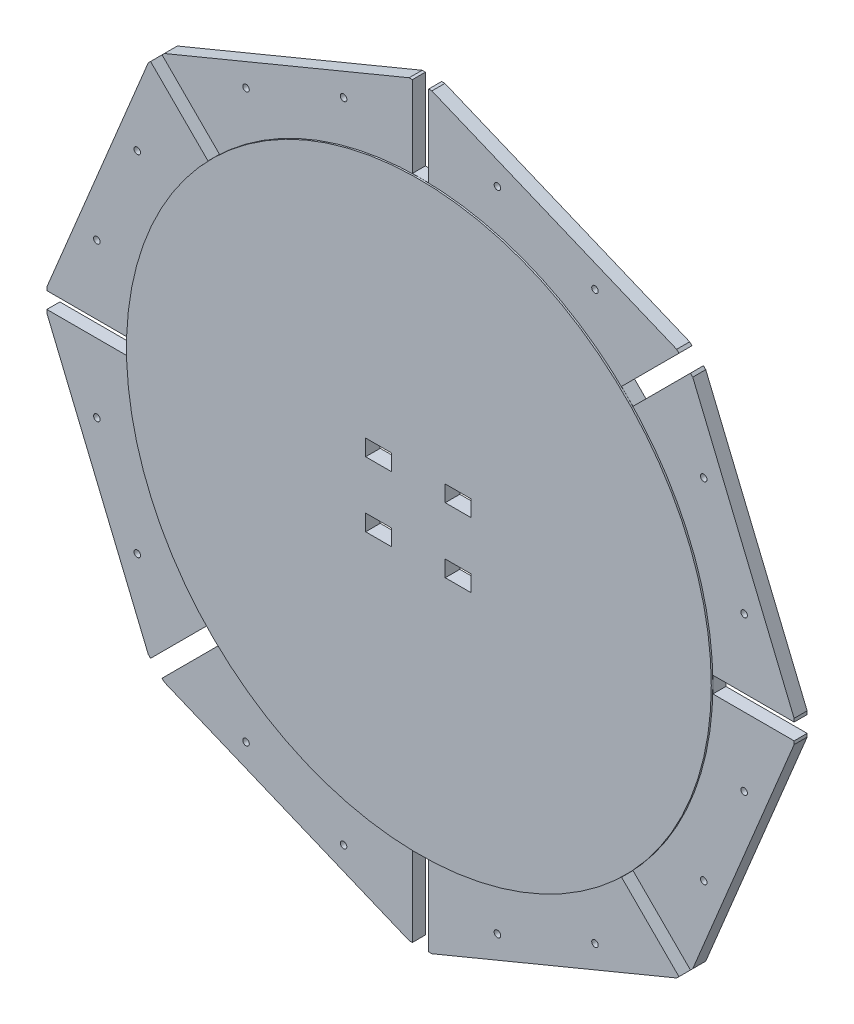
SolidWorks part; units mm, degrees
ref_plane "Front Plane" through (0, 0, 0) normal (0, 0, 1) x (1, 0, 0)
ref_plane "Top Plane" through (0, 0, 0) normal (0, 1, 0) x (1, 0, 0)
ref_plane "Right Plane" through (0, 0, 0) normal (1, 0, 0) x (0, 0, -1)
sketch "Sketch1" plane through (0, 0, 0) normal (0, 0, 1) x (1, 0, 0)
  line L0 (5, 230) -> (5, 180)
  line L1 (5, 180) -> (-5, 180)
  line L2 (-5, 180) -> (-5, 230)
  line L3 (-5, 230) -> (-7, 230)
  line L4 (-7, 230) -> (-157.6848, 167.5843)
  line L5 (-157.6848, 167.5843) -> (-159.099, 166.1701)
  line L6 (-159.099, 166.1701) -> (-123.7437, 130.8148)
  line L7 (-123.7437, 130.8148) -> (-130.8148, 123.7437)
  line L8 (-130.8148, 123.7437) -> (-166.1701, 159.099)
  line L9 (-166.1701, 159.099) -> (-167.5843, 157.6848)
  line L10 (-167.5843, 157.6848) -> (-230, 7)
  line L11 (-230, 7) -> (-230, 5)
  line L12 (-230, 5) -> (-180, 5)
  line L13 (-180, 5) -> (-180, -5)
  line L14 (-180, -5) -> (-230, -5)
  line L15 (-230, -5) -> (-230, -7)
  line L16 (-230, -7) -> (-167.5843, -157.6848)
  line L17 (-167.5843, -157.6848) -> (-166.1701, -159.099)
  line L18 (-166.1701, -159.099) -> (-130.8148, -123.7437)
  line L19 (-130.8148, -123.7437) -> (-123.7437, -130.8148)
  line L20 (-123.7437, -130.8148) -> (-159.099, -166.1701)
  line L21 (-159.099, -166.1701) -> (-157.6848, -167.5843)
  line L22 (-157.6848, -167.5843) -> (-7, -230)
  line L23 (-7, -230) -> (-5, -230)
  line L24 (-5, -230) -> (-5, -180)
  line L25 (-5, -180) -> (5, -180)
  line L26 (5, -180) -> (5, -230)
  line L27 (5, -230) -> (7, -230)
  line L28 (7, -230) -> (157.6848, -167.5843)
  line L29 (157.6848, -167.5843) -> (159.099, -166.1701)
  line L30 (159.099, -166.1701) -> (123.7437, -130.8148)
  line L31 (123.7437, -130.8148) -> (130.8148, -123.7437)
  line L32 (130.8148, -123.7437) -> (166.1701, -159.099)
  line L33 (166.1701, -159.099) -> (167.5843, -157.6848)
  line L34 (167.5843, -157.6848) -> (230, -7)
  line L35 (230, -7) -> (230, -5)
  line L36 (230, -5) -> (180, -5)
  line L37 (180, -5) -> (180, 5)
  line L38 (180, 5) -> (230, 5)
  line L39 (230, 5) -> (230, 7)
  line L40 (230, 7) -> (167.5843, 157.6848)
  line L41 (167.5843, 157.6848) -> (166.1701, 159.099)
  line L42 (166.1701, 159.099) -> (130.8148, 123.7437)
  line L43 (130.8148, 123.7437) -> (123.7437, 130.8148)
  line L44 (123.7437, 130.8148) -> (159.099, 166.1701)
  line L45 (159.099, 166.1701) -> (157.6848, 167.5843)
  line L46 (157.6848, 167.5843) -> (7, 230)
  line L47 (7, 230) -> (5, 230)
  line L48 (0, 180) -> (0, -180) construction
  line L49 (-180, 0) -> (180, 0) construction
  dimension "D1" = 163.1001
  dimension "D2" = 10
extrude "Boss-Extrude1" add sketch "Sketch1" along normal blind 8
sketch "Sketch2" plane through (0, 0, 8) normal (0, 0, 1) x (1, 0, 0)
  line L0 (5, 180) -> (-5, 180) construction
  circle A0 centre (0, 0) radius 180
  point P0 (0, 180)
extrude "Boss-Extrude2" add sketch "Sketch2" along normal blind 1
sketch "Sketch3" plane through (0, 0, 8) normal (0, 0, 1) x (1, 0, 0)
  circle A0 centre (107.3978, 174.3545) radius 2
  circle A1 centre (47.3456, 199.2289) radius 2
  circle A3 centre (199.2289, 47.3456) radius 2
  circle A4 centre (174.3545, 107.3978) radius 2
  circle A5 centre (174.3545, -107.3978) radius 2
  circle A6 centre (199.2289, -47.3456) radius 2
  circle A7 centre (47.3456, -199.2289) radius 2
  circle A8 centre (107.3978, -174.3545) radius 2
  circle A9 centre (-107.3978, -174.3545) radius 2
  circle A10 centre (-47.3456, -199.2289) radius 2
  circle A11 centre (-199.2289, -47.3456) radius 2
  circle A12 centre (-174.3545, -107.3978) radius 2
  circle A13 centre (-174.3545, 107.3978) radius 2
  circle A14 centre (-199.2289, 47.3456) radius 2
  circle A15 centre (-47.3456, 199.2289) radius 2
  circle A16 centre (-107.3978, 174.3545) radius 2
  point P37 (0, 0)
  dimension "D1" = 8
extrude "Cut-Extrude1" cut sketch "Sketch3" against normal up to next
sketch "Sketch4" plane through (0, 0, 0) normal (0, 0, -1) x (-1, 0, 0)
  circle A0 centre (-0.5579, 0.279) radius 45
  dimension "D1" = 90
sketch "Sketch5" plane through (0, 0, 0) normal (0, 0, -1) x (-1, 0, 0)
  line L1 (-32.221, -24.4421) -> (-16.221, -24.4421)
  line L2 (-32.221, -24.4421) -> (-32.221, -14.4421)
  line L3 (-32.221, -14.4421) -> (-16.221, -14.4421)
  line L4 (-16.221, -24.4421) -> (-16.221, -14.4421)
  line L5 (-32.221, 15.5579) -> (-16.221, 15.5579)
  line L6 (-32.221, 15.5579) -> (-32.221, 25.5579)
  line L7 (-32.221, 25.5579) -> (-16.221, 25.5579)
  line L8 (-16.221, 15.5579) -> (-16.221, 25.5579)
  line L9 (16.779, 15.5579) -> (32.779, 15.5579)
  line L10 (16.779, 15.5579) -> (16.779, 25.5579)
  line L11 (16.779, 25.5579) -> (32.779, 25.5579)
  line L12 (32.779, 15.5579) -> (32.779, 25.5579)
  line L13 (16.779, -24.4421) -> (32.779, -24.4421)
  line L14 (16.779, -24.4421) -> (16.779, -14.4421)
  line L15 (16.779, -14.4421) -> (32.779, -14.4421)
  line L16 (32.779, -24.4421) -> (32.779, -14.4421)
  dimension "D1" = 16
extrude "Cut-Extrude2" cut sketch "Sketch5" against normal up to next
